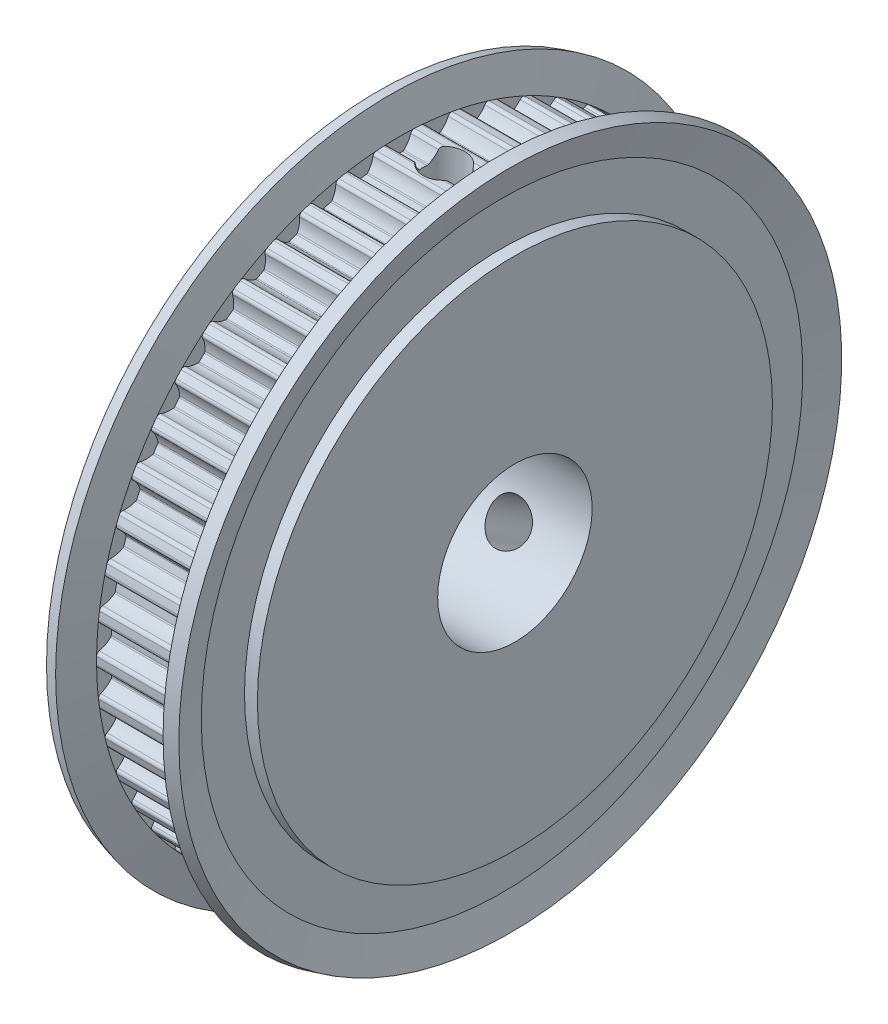
SolidWorks part; units mm, degrees
ref_plane "正面" through (0, 0, 0) normal (0, 0, 1) x (1, 0, 0)
ref_plane "平面" through (0, 0, 0) normal (0, 1, 0) x (1, 0, 0)
ref_plane "右側面" through (0, 0, 0) normal (1, 0, 0) x (0, 0, -1)
ref_plane "平面1" through (0, 0, 0) normal (0, 0, 1) x (1, 0, 0)
sketch "ｽｹｯﾁ1" plane through (0, 0, 0) normal (0, 0, 1) x (1, 0, 0)
  line L0 (0, 0) -> (0, 20)
  line L1 (0, 20) -> (1, 20)
  line L2 (1, 20) -> (1, 23.3583)
  line L3 (1, 23.3583) -> (0.3615, 25.7412)
  line L4 (0.3615, 25.7412) -> (1.3274, 26)
  line L5 (1.3274, 26) -> (2, 23.49)
  line L6 (2, 23.49) -> (9, 23.49)
  line L7 (9, 23.49) -> (9.6726, 26)
  line L8 (9.6726, 26) -> (10.6385, 25.7412)
  line L9 (10.6385, 25.7412) -> (10, 23.3583)
  line L10 (10, 23.3583) -> (10, 20)
  line L11 (10, 20) -> (11, 20)
  line L12 (11, 20) -> (11, 0)
  line L13 (11, 0) -> (0, 0)
  line L14 (11, 0) -> (0, 0) construction
revolve "回転1" add sketch "ｽｹｯﾁ1" angle 360 about L14
ref_plane "平面2" through (0, 0, 0) normal (0, 0, 1) x (1, 0, 0)
sketch "ｽｹｯﾁ2" plane through (0, 0, 0) normal (0, 0, 1) x (1, 0, 0)
  line L0 (0, 0) -> (0, 6)
  line L1 (0, 6) -> (11, 6)
  line L2 (11, 6) -> (11, 0)
  line L3 (11, 0) -> (0, 0)
  line L4 (11, 0) -> (0, 0) construction
revolve "ｶｯﾄ - 回転1" cut sketch "ｽｹｯﾁ2" angle 360 about L4
ref_plane "平面3" through (2, 0, 0) normal (1, 0, 0) x (0, 0, -1)
sketch "ｽｹｯﾁ3" plane through (2, 0, 0) normal (1, 0, 0) x (0, 0, -1)
  circle A0 centre (0, 0) radius 28.49
  arc A1 (-23.4883, 0.2846) -> (-23.4883, -0.2846) centre (0, 0) ccw
  arc A2 (-23.4883, -0.2846) -> (-23.2752, -0.5531) centre (-23.2083, -0.2812) ccw
  arc A3 (-23.2752, -0.5531) -> (-22.3989, -1.0274) centre (-23.7468, -2.4709) cw
  arc A4 (-22.3989, -1.0274) -> (-22.3515, -1.1295) centre (-22.5013, -1.137) cw
  arc A5 (-22.3515, -1.1295) -> (-22.3168, -1.6808) centre (0, 0) ccw
  arc A6 (-22.3168, -1.6808) -> (-22.3511, -1.788) centre (-22.4664, -1.6921) cw
  arc A7 (-22.3511, -1.788) -> (-23.1609, -2.3684) centre (-23.8692, -0.5248) cw
  arc A8 (-23.1609, -2.3684) -> (-23.3387, -2.6615) centre (-23.0605, -2.6298) ccw
  arc A9 (-23.3387, -2.6615) -> (-23.2674, -3.2262) centre (0, 0) ccw
  arc A10 (-23.2674, -3.2262) -> (-23.0223, -3.4659) centre (-22.99, -3.1877) ccw
  arc A11 (-23.0223, -3.4659) -> (-22.0935, -3.8266) centre (-23.2498, -5.4277) cw
  arc A12 (-22.0935, -3.8266) -> (-22.0337, -3.9219) centre (-22.1814, -3.9482) cw
  arc A13 (-22.0337, -3.9219) -> (-21.9302, -4.4646) centre (0, 0) ccw
  arc A14 (-21.9302, -4.4646) -> (-21.9507, -4.5753) centre (-22.0771, -4.4945) cw
  arc A15 (-21.9507, -4.5753) -> (-22.6815, -5.2526) centre (-23.6152, -3.5123) cw
  arc A16 (-22.6815, -5.2526) -> (-22.8211, -5.5657) centre (-22.5491, -5.4993) ccw
  arc A17 (-22.8211, -5.5657) -> (-22.6796, -6.1169) centre (0, 0) ccw
  arc A18 (-22.6796, -6.1169) -> (-22.4064, -6.324) centre (-22.4092, -6.044) ccw
  arc A19 (-22.4064, -6.324) -> (-21.4397, -6.5655) centre (-22.3862, -8.2989) cw
  arc A20 (-21.4397, -6.5655) -> (-21.3684, -6.6526) centre (-21.5116, -6.6971) cw
  arc A21 (-21.3684, -6.6526) -> (-21.1977, -7.178) centre (0, 0) ccw
  arc A22 (-21.1977, -7.178) -> (-21.2042, -7.2904) centre (-21.3397, -7.2261) cw
  arc A23 (-21.2042, -7.2904) -> (-21.8443, -8.0539) centre (-22.9888, -6.4443) cw
  arc A24 (-21.8443, -8.0539) -> (-21.9436, -8.382) centre (-21.682, -8.2821) ccw
  arc A25 (-21.9436, -8.382) -> (-21.7341, -8.9112) centre (0, 0) ccw
  arc A26 (-21.7341, -8.9112) -> (-21.4371, -9.0824) centre (-21.475, -8.805) ccw
  arc A27 (-21.4371, -9.0824) -> (-20.4478, -9.2008) centre (-21.1696, -11.0392) cw
  arc A28 (-20.4478, -9.2008) -> (-20.3661, -9.2783) centre (-20.5026, -9.3405) cw
  arc A29 (-20.3661, -9.2783) -> (-20.1309, -9.7782) centre (0, 0) ccw
  arc A30 (-20.1309, -9.7782) -> (-20.1233, -9.8905) centre (-20.2658, -9.8437) cw
  arc A31 (-20.1233, -9.8905) -> (-20.6626, -10.7282) centre (-21.9999, -9.2748) cw
  arc A32 (-20.6626, -10.7282) -> (-20.72, -11.0662) centre (-20.473, -10.9343) ccw
  arc A33 (-20.72, -11.0662) -> (-20.4458, -11.5649) centre (0, 0) ccw
  arc A34 (-20.4458, -11.5649) -> (-20.1297, -11.6976) centre (-20.2021, -11.4271) ccw
  arc A35 (-20.1297, -11.6976) -> (-19.1334, -11.6911) centre (-19.6191, -13.6054) cw
  arc A36 (-19.1334, -11.6911) -> (-19.0426, -11.7577) centre (-19.1703, -11.8365) cw
  arc A37 (-19.0426, -11.7577) -> (-18.7466, -12.2241) centre (0, 0) ccw
  arc A38 (-18.7466, -12.2241) -> (-18.725, -12.3346) centre (-18.8723, -12.3061) cw
  arc A39 (-18.725, -12.3346) -> (-19.1551, -13.2333) centre (-20.6639, -11.959) cw
  arc A40 (-19.1551, -13.2333) -> (-19.1697, -13.5758) centre (-18.9412, -13.414) ccw
  arc A41 (-19.1697, -13.5758) -> (-18.8351, -14.0363) centre (0, 0) ccw
  arc A42 (-18.8351, -14.0363) -> (-18.5049, -14.1283) centre (-18.6106, -13.869) ccw
  arc A43 (-18.5049, -14.1283) -> (-17.5172, -13.9969) centre (-17.7592, -15.9571) cw
  arc A44 (-17.5172, -13.9969) -> (-17.4189, -14.0516) centre (-17.5356, -14.1458) cw
  arc A45 (-17.4189, -14.0516) -> (-17.0667, -14.4773) centre (0, 0) ccw
  arc A46 (-17.0667, -14.4773) -> (-17.0314, -14.5842) centre (-17.1811, -14.5743) cw
  arc A47 (-17.0314, -14.5842) -> (-17.3455, -15.5298) centre (-19.0021, -14.4546) cw
  arc A48 (-17.3455, -15.5298) -> (-17.317, -15.8714) centre (-17.1106, -15.6822) ccw
  arc A49 (-17.317, -15.8714) -> (-16.9274, -16.2863) centre (0, 0) ccw
  arc A50 (-16.9274, -16.2863) -> (-16.5882, -16.3361) centre (-16.7256, -16.0922) ccw
  arc A51 (-16.5882, -16.3361) -> (-15.6248, -16.082) centre (-15.6192, -18.057) cw
  arc A52 (-15.6248, -16.082) -> (-15.5204, -16.124) centre (-15.6244, -16.232) cw
  arc A53 (-15.5204, -16.124) -> (-15.1176, -16.5022) centre (0, 0) ccw
  arc A54 (-15.1176, -16.5022) -> (-15.0692, -16.6038) centre (-15.219, -16.6128) cw
  arc A55 (-15.0692, -16.6038) -> (-15.2623, -17.5813) centre (-17.0407, -16.7222) cw
  arc A56 (-15.2623, -17.5813) -> (-15.1913, -17.9166) centre (-15.0102, -17.7031) ccw
  arc A57 (-15.1913, -17.9166) -> (-14.7527, -18.2794) centre (0, 0) ccw
  arc A58 (-14.7527, -18.2794) -> (-14.41, -18.2864) centre (-14.5769, -18.0615) ccw
  arc A59 (-14.41, -18.2864) -> (-13.486, -17.9135) centre (-13.2329, -19.8723) cw
  arc A60 (-13.486, -17.9135) -> (-13.3771, -17.9421) centre (-13.4668, -18.0623) cw
  arc A61 (-13.3771, -17.9421) -> (-12.9302, -18.2668) centre (0, 0) ccw
  arc A62 (-12.9302, -18.2668) -> (-12.8694, -18.3615) centre (-13.0168, -18.3892) cw
  arc A63 (-12.8694, -18.3615) -> (-12.9384, -19.3555) centre (-14.8105, -18.7261) cw
  arc A64 (-12.9384, -19.3555) -> (-12.8259, -19.6793) centre (-12.673, -19.4447) ccw
  arc A65 (-12.8259, -19.6793) -> (-12.3454, -19.9843) centre (0, 0) ccw
  arc A66 (-12.3454, -19.9843) -> (-12.0045, -19.9482) centre (-12.1982, -19.7461) ccw
  arc A67 (-12.0045, -19.9482) -> (-11.1345, -19.4625) centre (-10.6379, -21.3741) cw
  arc A68 (-11.1345, -19.4625) -> (-11.0229, -19.4772) centre (-11.0968, -19.6077) cw
  arc A69 (-11.0229, -19.4772) -> (-10.5388, -19.7433) centre (0, 0) ccw
  arc A70 (-10.5388, -19.7433) -> (-10.4666, -19.8297) centre (-10.6094, -19.8757) cw
  arc A71 (-10.4666, -19.8297) -> (-10.4105, -20.8245) centre (-12.3467, -20.4347) cw
  arc A72 (-10.4105, -20.8245) -> (-10.2583, -21.1317) centre (-10.136, -20.8798) ccw
  arc A73 (-10.2583, -21.1317) -> (-9.7433, -21.374) centre (0, 0) ccw
  arc A74 (-9.7433, -21.374) -> (-9.4096, -21.2955) centre (-9.6272, -21.1192) ccw
  arc A75 (-9.4096, -21.2955) -> (-8.6074, -20.7046) centre (-7.8751, -22.5388) cw
  arc A76 (-8.6074, -20.7046) -> (-8.4948, -20.7051) centre (-8.5518, -20.8439) cw
  arc A77 (-8.4948, -20.7051) -> (-7.9812, -20.9085) centre (0, 0) ccw
  arc A78 (-7.9812, -20.9085) -> (-7.8987, -20.9852) centre (-8.0347, -21.0486) cw
  arc A79 (-7.8987, -20.9852) -> (-7.7184, -21.9651) centre (-9.6882, -21.821) cw
  arc A80 (-7.7184, -21.9651) -> (-7.5289, -22.2507) centre (-7.4392, -21.9855) ccw
  arc A81 (-7.5289, -22.2507) -> (-6.9876, -22.4266) centre (0, 0) ccw
  arc A82 (-6.9876, -22.4266) -> (-6.6664, -22.3069) centre (-6.9043, -22.1593) ccw
  arc A83 (-6.6664, -22.3069) -> (-5.9445, -21.6201) centre (-4.9881, -23.3481) cw
  arc A84 (-5.9445, -21.6201) -> (-5.8328, -21.6065) centre (-5.8719, -21.7514) cw
  arc A85 (-5.8328, -21.6065) -> (-5.2977, -21.7439) centre (0, 0) ccw
  arc A86 (-5.2977, -21.7439) -> (-5.2063, -21.8097) centre (-5.3332, -21.8897) cw
  arc A87 (-5.2063, -21.8097) -> (-4.9046, -22.7593) centre (-6.8769, -22.8632) cw
  arc A88 (-4.9046, -22.7593) -> (-4.6808, -23.0189) centre (-4.625, -22.7445) ccw
  arc A89 (-4.6808, -23.0189) -> (-4.1217, -23.1256) centre (0, 0) ccw
  arc A90 (-4.1217, -23.1256) -> (-3.818, -22.9665) centre (-4.0726, -22.8499) ccw
  arc A91 (-3.818, -22.9665) -> (-3.188, -22.1947) centre (-2.0225, -23.7892) cw
  arc A92 (-3.188, -22.1947) -> (-3.0788, -22.1672) centre (-3.0994, -22.3158) cw
  arc A93 (-3.0788, -22.1672) -> (-2.5307, -22.2365) centre (0, 0) ccw
  arc A94 (-2.5307, -22.2365) -> (-2.4318, -22.2902) centre (-2.5476, -22.3855) cw
  arc A95 (-2.4318, -22.2902) -> (-2.0135, -23.1945) centre (-3.9571, -23.5448) cw
  arc A96 (-2.0135, -23.1945) -> (-1.7589, -23.4241) centre (-1.7379, -23.1448) ccw
  arc A97 (-1.7589, -23.4241) -> (-1.1908, -23.4598) centre (0, 0) ccw
  arc A98 (-1.1908, -23.4598) -> (-0.9095, -23.264) centre (-1.1766, -23.1802) ccw
  arc A99 (-0.9095, -23.264) -> (-0.3811, -22.4192) centre (0.975, -23.8551) cw
  arc A100 (-0.3811, -22.4192) -> (-0.2762, -22.3783) centre (-0.2781, -22.5283) cw
  arc A101 (-0.2762, -22.3783) -> (0.2762, -22.3783) centre (0, 0) ccw
  arc A102 (0.2762, -22.3783) -> (0.3811, -22.4192) centre (0.2781, -22.5283) cw
  arc A103 (0.3811, -22.4192) -> (0.9095, -23.264) centre (-0.975, -23.8551) cw
  arc A104 (0.9095, -23.264) -> (1.1908, -23.4598) centre (1.1766, -23.1802) ccw
  arc A105 (1.1908, -23.4598) -> (1.7589, -23.4241) centre (0, 0) ccw
  arc A106 (1.7589, -23.4241) -> (2.0135, -23.1945) centre (1.7379, -23.1448) ccw
  arc A107 (2.0135, -23.1945) -> (2.4318, -22.2902) centre (3.9571, -23.5448) cw
  arc A108 (2.4318, -22.2902) -> (2.5307, -22.2365) centre (2.5476, -22.3855) cw
  arc A109 (2.5307, -22.2365) -> (3.0788, -22.1672) centre (0, 0) ccw
  arc A110 (3.0788, -22.1672) -> (3.188, -22.1947) centre (3.0994, -22.3158) cw
  arc A111 (3.188, -22.1947) -> (3.818, -22.9665) centre (2.0225, -23.7892) cw
  arc A112 (3.818, -22.9665) -> (4.1217, -23.1256) centre (4.0726, -22.8499) ccw
  arc A113 (4.1217, -23.1256) -> (4.6808, -23.0189) centre (0, 0) ccw
  arc A114 (4.6808, -23.0189) -> (4.9046, -22.7593) centre (4.625, -22.7445) ccw
  arc A115 (4.9046, -22.7593) -> (5.2063, -21.8097) centre (6.8769, -22.8632) cw
  arc A116 (5.2063, -21.8097) -> (5.2977, -21.7439) centre (5.3332, -21.8897) cw
  arc A117 (5.2977, -21.7439) -> (5.8328, -21.6065) centre (0, 0) ccw
  arc A118 (5.8328, -21.6065) -> (5.9445, -21.6201) centre (5.8719, -21.7514) cw
  arc A119 (5.9445, -21.6201) -> (6.6664, -22.3069) centre (4.9881, -23.3481) cw
  arc A120 (6.6664, -22.3069) -> (6.9876, -22.4266) centre (6.9043, -22.1593) ccw
  arc A121 (6.9876, -22.4266) -> (7.5289, -22.2507) centre (0, 0) ccw
  arc A122 (7.5289, -22.2507) -> (7.7184, -21.9651) centre (7.4392, -21.9855) ccw
  arc A123 (7.7184, -21.9651) -> (7.8987, -20.9852) centre (9.6882, -21.821) cw
  arc A124 (7.8987, -20.9852) -> (7.9812, -20.9085) centre (8.0347, -21.0486) cw
  arc A125 (7.9812, -20.9085) -> (8.4948, -20.7051) centre (0, 0) ccw
  arc A126 (8.4948, -20.7051) -> (8.6074, -20.7046) centre (8.5518, -20.8439) cw
  arc A127 (8.6074, -20.7046) -> (9.4096, -21.2955) centre (7.8751, -22.5388) cw
  arc A128 (9.4096, -21.2955) -> (9.7433, -21.374) centre (9.6272, -21.1192) ccw
  arc A129 (9.7433, -21.374) -> (10.2583, -21.1317) centre (0, 0) ccw
  arc A130 (10.2583, -21.1317) -> (10.4105, -20.8245) centre (10.136, -20.8798) ccw
  arc A131 (10.4105, -20.8245) -> (10.4666, -19.8297) centre (12.3467, -20.4347) cw
  arc A132 (10.4666, -19.8297) -> (10.5388, -19.7433) centre (10.6094, -19.8757) cw
  arc A133 (10.5388, -19.7433) -> (11.0229, -19.4772) centre (0, 0) ccw
  arc A134 (11.0229, -19.4772) -> (11.1345, -19.4625) centre (11.0968, -19.6077) cw
  arc A135 (11.1345, -19.4625) -> (12.0045, -19.9482) centre (10.6379, -21.3741) cw
  arc A136 (12.0045, -19.9482) -> (12.3454, -19.9843) centre (12.1982, -19.7461) ccw
  arc A137 (12.3454, -19.9843) -> (12.8259, -19.6793) centre (0, 0) ccw
  arc A138 (12.8259, -19.6793) -> (12.9384, -19.3555) centre (12.673, -19.4447) ccw
  arc A139 (12.9384, -19.3555) -> (12.8694, -18.3615) centre (14.8105, -18.7261) cw
  arc A140 (12.8694, -18.3615) -> (12.9302, -18.2668) centre (13.0168, -18.3892) cw
  arc A141 (12.9302, -18.2668) -> (13.3771, -17.9421) centre (0, 0) ccw
  arc A142 (13.3771, -17.9421) -> (13.486, -17.9135) centre (13.4668, -18.0623) cw
  arc A143 (13.486, -17.9135) -> (14.41, -18.2864) centre (13.2329, -19.8723) cw
  arc A144 (14.41, -18.2864) -> (14.7527, -18.2794) centre (14.5769, -18.0615) ccw
  arc A145 (14.7527, -18.2794) -> (15.1913, -17.9166) centre (0, 0) ccw
  arc A146 (15.1913, -17.9166) -> (15.2623, -17.5813) centre (15.0102, -17.7031) ccw
  arc A147 (15.2623, -17.5813) -> (15.0692, -16.6038) centre (17.0407, -16.7222) cw
  arc A148 (15.0692, -16.6038) -> (15.1176, -16.5022) centre (15.219, -16.6128) cw
  arc A149 (15.1176, -16.5022) -> (15.5204, -16.124) centre (0, 0) ccw
  arc A150 (15.5204, -16.124) -> (15.6248, -16.082) centre (15.6244, -16.232) cw
  arc A151 (15.6248, -16.082) -> (16.5882, -16.3361) centre (15.6192, -18.057) cw
  arc A152 (16.5882, -16.3361) -> (16.9274, -16.2863) centre (16.7256, -16.0922) ccw
  arc A153 (16.9274, -16.2863) -> (17.317, -15.8714) centre (0, 0) ccw
  arc A154 (17.317, -15.8714) -> (17.3455, -15.5298) centre (17.1106, -15.6822) ccw
  arc A155 (17.3455, -15.5298) -> (17.0314, -14.5842) centre (19.0021, -14.4546) cw
  arc A156 (17.0314, -14.5842) -> (17.0667, -14.4773) centre (17.1811, -14.5743) cw
  arc A157 (17.0667, -14.4773) -> (17.4189, -14.0516) centre (0, 0) ccw
  arc A158 (17.4189, -14.0516) -> (17.5172, -13.9969) centre (17.5356, -14.1458) cw
  arc A159 (17.5172, -13.9969) -> (18.5049, -14.1283) centre (17.7592, -15.9571) cw
  arc A160 (18.5049, -14.1283) -> (18.8351, -14.0363) centre (18.6106, -13.869) ccw
  arc A161 (18.8351, -14.0363) -> (19.1697, -13.5758) centre (0, 0) ccw
  arc A162 (19.1697, -13.5758) -> (19.1551, -13.2333) centre (18.9412, -13.414) ccw
  arc A163 (19.1551, -13.2333) -> (18.725, -12.3346) centre (20.6639, -11.959) cw
  arc A164 (18.725, -12.3346) -> (18.7466, -12.2241) centre (18.8723, -12.3061) cw
  arc A165 (18.7466, -12.2241) -> (19.0426, -11.7577) centre (0, 0) ccw
  arc A166 (19.0426, -11.7577) -> (19.1334, -11.6911) centre (19.1703, -11.8365) cw
  arc A167 (19.1334, -11.6911) -> (20.1297, -11.6976) centre (19.6191, -13.6054) cw
  arc A168 (20.1297, -11.6976) -> (20.4458, -11.5649) centre (20.2021, -11.4271) ccw
  arc A169 (20.4458, -11.5649) -> (20.72, -11.0662) centre (0, 0) ccw
  arc A170 (20.72, -11.0662) -> (20.6626, -10.7282) centre (20.473, -10.9343) ccw
  arc A171 (20.6626, -10.7282) -> (20.1233, -9.8905) centre (21.9999, -9.2748) cw
  arc A172 (20.1233, -9.8905) -> (20.1309, -9.7782) centre (20.2658, -9.8437) cw
  arc A173 (20.1309, -9.7782) -> (20.3661, -9.2783) centre (0, 0) ccw
  arc A174 (20.3661, -9.2783) -> (20.4478, -9.2008) centre (20.5026, -9.3405) cw
  arc A175 (20.4478, -9.2008) -> (21.4371, -9.0824) centre (21.1696, -11.0392) cw
  arc A176 (21.4371, -9.0824) -> (21.7341, -8.9112) centre (21.475, -8.805) ccw
  arc A177 (21.7341, -8.9112) -> (21.9436, -8.382) centre (0, 0) ccw
  arc A178 (21.9436, -8.382) -> (21.8443, -8.0539) centre (21.682, -8.2821) ccw
  arc A179 (21.8443, -8.0539) -> (21.2042, -7.2904) centre (22.9888, -6.4443) cw
  arc A180 (21.2042, -7.2904) -> (21.1977, -7.178) centre (21.3397, -7.2261) cw
  arc A181 (21.1977, -7.178) -> (21.3684, -6.6526) centre (0, 0) ccw
  arc A182 (21.3684, -6.6526) -> (21.4397, -6.5655) centre (21.5116, -6.6971) cw
  arc A183 (21.4397, -6.5655) -> (22.4064, -6.324) centre (22.3862, -8.2989) cw
  arc A184 (22.4064, -6.324) -> (22.6796, -6.1169) centre (22.4092, -6.044) ccw
  arc A185 (22.6796, -6.1169) -> (22.8211, -5.5657) centre (0, 0) ccw
  arc A186 (22.8211, -5.5657) -> (22.6815, -5.2526) centre (22.5491, -5.4993) ccw
  arc A187 (22.6815, -5.2526) -> (21.9507, -4.5753) centre (23.6152, -3.5123) cw
  arc A188 (21.9507, -4.5753) -> (21.9302, -4.4646) centre (22.0771, -4.4945) cw
  arc A189 (21.9302, -4.4646) -> (22.0337, -3.9219) centre (0, 0) ccw
  arc A190 (22.0337, -3.9219) -> (22.0935, -3.8266) centre (22.1814, -3.9482) cw
  arc A191 (22.0935, -3.8266) -> (23.0223, -3.4659) centre (23.2498, -5.4277) cw
  arc A192 (23.0223, -3.4659) -> (23.2674, -3.2262) centre (22.99, -3.1877) ccw
  arc A193 (23.2674, -3.2262) -> (23.3387, -2.6615) centre (0, 0) ccw
  arc A194 (23.3387, -2.6615) -> (23.1609, -2.3684) centre (23.0605, -2.6298) ccw
  arc A195 (23.1609, -2.3684) -> (22.3511, -1.788) centre (23.8692, -0.5248) cw
  arc A196 (22.3511, -1.788) -> (22.3168, -1.6808) centre (22.4664, -1.6921) cw
  arc A197 (22.3168, -1.6808) -> (22.3515, -1.1295) centre (0, 0) ccw
  arc A198 (22.3515, -1.1295) -> (22.3989, -1.0274) centre (22.5013, -1.137) cw
  arc A199 (22.3989, -1.0274) -> (23.2752, -0.5531) centre (23.7468, -2.4709) cw
  arc A200 (23.2752, -0.5531) -> (23.4883, -0.2846) centre (23.2083, -0.2812) ccw
  arc A201 (23.4883, -0.2846) -> (23.4883, 0.2846) centre (0, 0) ccw
  arc A202 (23.4883, 0.2846) -> (23.2752, 0.5531) centre (23.2083, 0.2812) ccw
  arc A203 (23.2752, 0.5531) -> (22.3989, 1.0274) centre (23.7468, 2.4709) cw
  arc A204 (22.3989, 1.0274) -> (22.3515, 1.1295) centre (22.5013, 1.137) cw
  arc A205 (22.3515, 1.1295) -> (22.3168, 1.6808) centre (0, 0) ccw
  arc A206 (22.3168, 1.6808) -> (22.3511, 1.788) centre (22.4664, 1.6921) cw
  arc A207 (22.3511, 1.788) -> (23.1609, 2.3684) centre (23.8692, 0.5248) cw
  arc A208 (23.1609, 2.3684) -> (23.3387, 2.6615) centre (23.0605, 2.6298) ccw
  arc A209 (23.3387, 2.6615) -> (23.2674, 3.2262) centre (0, 0) ccw
  arc A210 (23.2674, 3.2262) -> (23.0223, 3.4659) centre (22.99, 3.1877) ccw
  arc A211 (23.0223, 3.4659) -> (22.0935, 3.8266) centre (23.2498, 5.4277) cw
  arc A212 (22.0935, 3.8266) -> (22.0337, 3.9219) centre (22.1814, 3.9482) cw
  arc A213 (22.0337, 3.9219) -> (21.9302, 4.4646) centre (0, 0) ccw
  arc A214 (21.9302, 4.4646) -> (21.9507, 4.5753) centre (22.0771, 4.4945) cw
  arc A215 (21.9507, 4.5753) -> (22.6815, 5.2526) centre (23.6152, 3.5123) cw
  arc A216 (22.6815, 5.2526) -> (22.8211, 5.5657) centre (22.5491, 5.4993) ccw
  arc A217 (22.8211, 5.5657) -> (22.6796, 6.1169) centre (0, 0) ccw
  arc A218 (22.6796, 6.1169) -> (22.4064, 6.324) centre (22.4092, 6.044) ccw
  arc A219 (22.4064, 6.324) -> (21.4397, 6.5655) centre (22.3862, 8.2989) cw
  arc A220 (21.4397, 6.5655) -> (21.3684, 6.6526) centre (21.5116, 6.6971) cw
  arc A221 (21.3684, 6.6526) -> (21.1977, 7.178) centre (0, 0) ccw
  arc A222 (21.1977, 7.178) -> (21.2042, 7.2904) centre (21.3397, 7.2261) cw
  arc A223 (21.2042, 7.2904) -> (21.8443, 8.0539) centre (22.9888, 6.4443) cw
  arc A224 (21.8443, 8.0539) -> (21.9436, 8.382) centre (21.682, 8.2821) ccw
  arc A225 (21.9436, 8.382) -> (21.7341, 8.9112) centre (0, 0) ccw
  arc A226 (21.7341, 8.9112) -> (21.4371, 9.0824) centre (21.475, 8.805) ccw
  arc A227 (21.4371, 9.0824) -> (20.4478, 9.2008) centre (21.1696, 11.0392) cw
  arc A228 (20.4478, 9.2008) -> (20.3661, 9.2783) centre (20.5026, 9.3405) cw
  arc A229 (20.3661, 9.2783) -> (20.1309, 9.7782) centre (0, 0) ccw
  arc A230 (20.1309, 9.7782) -> (20.1233, 9.8905) centre (20.2658, 9.8437) cw
  arc A231 (20.1233, 9.8905) -> (20.6626, 10.7282) centre (21.9999, 9.2748) cw
  arc A232 (20.6626, 10.7282) -> (20.72, 11.0662) centre (20.473, 10.9343) ccw
  arc A233 (20.72, 11.0662) -> (20.4458, 11.5649) centre (0, 0) ccw
  arc A234 (20.4458, 11.5649) -> (20.1297, 11.6976) centre (20.2021, 11.4271) ccw
  arc A235 (20.1297, 11.6976) -> (19.1334, 11.6911) centre (19.6191, 13.6054) cw
  arc A236 (19.1334, 11.6911) -> (19.0426, 11.7577) centre (19.1703, 11.8365) cw
  arc A237 (19.0426, 11.7577) -> (18.7466, 12.2241) centre (0, 0) ccw
  arc A238 (18.7466, 12.2241) -> (18.725, 12.3346) centre (18.8723, 12.3061) cw
  arc A239 (18.725, 12.3346) -> (19.1551, 13.2333) centre (20.6639, 11.959) cw
  arc A240 (19.1551, 13.2333) -> (19.1697, 13.5758) centre (18.9412, 13.414) ccw
  arc A241 (19.1697, 13.5758) -> (18.8351, 14.0363) centre (0, 0) ccw
  arc A242 (18.8351, 14.0363) -> (18.5049, 14.1283) centre (18.6106, 13.869) ccw
  arc A243 (18.5049, 14.1283) -> (17.5172, 13.9969) centre (17.7592, 15.9571) cw
  arc A244 (17.5172, 13.9969) -> (17.4189, 14.0516) centre (17.5356, 14.1458) cw
  arc A245 (17.4189, 14.0516) -> (17.0667, 14.4773) centre (0, 0) ccw
  arc A246 (17.0667, 14.4773) -> (17.0314, 14.5842) centre (17.1811, 14.5743) cw
  arc A247 (17.0314, 14.5842) -> (17.3455, 15.5298) centre (19.0021, 14.4546) cw
  arc A248 (17.3455, 15.5298) -> (17.317, 15.8714) centre (17.1106, 15.6822) ccw
  arc A249 (17.317, 15.8714) -> (16.9274, 16.2863) centre (0, 0) ccw
  arc A250 (16.9274, 16.2863) -> (16.5882, 16.3361) centre (16.7256, 16.0922) ccw
  arc A251 (16.5882, 16.3361) -> (15.6248, 16.082) centre (15.6192, 18.057) cw
  arc A252 (15.6248, 16.082) -> (15.5204, 16.124) centre (15.6244, 16.232) cw
  arc A253 (15.5204, 16.124) -> (15.1176, 16.5022) centre (0, 0) ccw
  arc A254 (15.1176, 16.5022) -> (15.0692, 16.6038) centre (15.219, 16.6128) cw
  arc A255 (15.0692, 16.6038) -> (15.2623, 17.5813) centre (17.0407, 16.7222) cw
  arc A256 (15.2623, 17.5813) -> (15.1913, 17.9166) centre (15.0102, 17.7031) ccw
  arc A257 (15.1913, 17.9166) -> (14.7527, 18.2794) centre (0, 0) ccw
  arc A258 (14.7527, 18.2794) -> (14.41, 18.2864) centre (14.5769, 18.0615) ccw
  arc A259 (14.41, 18.2864) -> (13.486, 17.9135) centre (13.2329, 19.8723) cw
  arc A260 (13.486, 17.9135) -> (13.3771, 17.9421) centre (13.4668, 18.0623) cw
  arc A261 (13.3771, 17.9421) -> (12.9302, 18.2668) centre (0, 0) ccw
  arc A262 (12.9302, 18.2668) -> (12.8694, 18.3615) centre (13.0168, 18.3892) cw
  arc A263 (12.8694, 18.3615) -> (12.9384, 19.3555) centre (14.8105, 18.7261) cw
  arc A264 (12.9384, 19.3555) -> (12.8259, 19.6793) centre (12.673, 19.4447) ccw
  arc A265 (12.8259, 19.6793) -> (12.3454, 19.9843) centre (0, 0) ccw
  arc A266 (12.3454, 19.9843) -> (12.0045, 19.9482) centre (12.1982, 19.7461) ccw
  arc A267 (12.0045, 19.9482) -> (11.1345, 19.4625) centre (10.6379, 21.3741) cw
  arc A268 (11.1345, 19.4625) -> (11.0229, 19.4772) centre (11.0968, 19.6077) cw
  arc A269 (11.0229, 19.4772) -> (10.5388, 19.7433) centre (0, 0) ccw
  arc A270 (10.5388, 19.7433) -> (10.4666, 19.8297) centre (10.6094, 19.8757) cw
  arc A271 (10.4666, 19.8297) -> (10.4105, 20.8245) centre (12.3467, 20.4347) cw
  arc A272 (10.4105, 20.8245) -> (10.2583, 21.1317) centre (10.136, 20.8798) ccw
  arc A273 (10.2583, 21.1317) -> (9.7433, 21.374) centre (0, 0) ccw
  arc A274 (9.7433, 21.374) -> (9.4096, 21.2955) centre (9.6272, 21.1192) ccw
  arc A275 (9.4096, 21.2955) -> (8.6074, 20.7046) centre (7.8751, 22.5388) cw
  arc A276 (8.6074, 20.7046) -> (8.4948, 20.7051) centre (8.5518, 20.8439) cw
  arc A277 (8.4948, 20.7051) -> (7.9812, 20.9085) centre (0, 0) ccw
  arc A278 (7.9812, 20.9085) -> (7.8987, 20.9852) centre (8.0347, 21.0486) cw
  arc A279 (7.8987, 20.9852) -> (7.7184, 21.9651) centre (9.6882, 21.821) cw
  arc A280 (7.7184, 21.9651) -> (7.5289, 22.2507) centre (7.4392, 21.9855) ccw
  arc A281 (7.5289, 22.2507) -> (6.9876, 22.4266) centre (0, 0) ccw
  arc A282 (6.9876, 22.4266) -> (6.6664, 22.3069) centre (6.9043, 22.1593) ccw
  arc A283 (6.6664, 22.3069) -> (5.9445, 21.6201) centre (4.9881, 23.3481) cw
  arc A284 (5.9445, 21.6201) -> (5.8328, 21.6065) centre (5.8719, 21.7514) cw
  arc A285 (5.8328, 21.6065) -> (5.2977, 21.7439) centre (0, 0) ccw
  arc A286 (5.2977, 21.7439) -> (5.2063, 21.8097) centre (5.3332, 21.8897) cw
  arc A287 (5.2063, 21.8097) -> (4.9046, 22.7593) centre (6.8769, 22.8632) cw
  arc A288 (4.9046, 22.7593) -> (4.6808, 23.0189) centre (4.625, 22.7445) ccw
  arc A289 (4.6808, 23.0189) -> (4.1217, 23.1256) centre (0, 0) ccw
  arc A290 (4.1217, 23.1256) -> (3.818, 22.9665) centre (4.0726, 22.8499) ccw
  arc A291 (3.818, 22.9665) -> (3.188, 22.1947) centre (2.0225, 23.7892) cw
  arc A292 (3.188, 22.1947) -> (3.0788, 22.1672) centre (3.0994, 22.3158) cw
  arc A293 (3.0788, 22.1672) -> (2.5307, 22.2365) centre (0, 0) ccw
  arc A294 (2.5307, 22.2365) -> (2.4318, 22.2902) centre (2.5476, 22.3855) cw
  arc A295 (2.4318, 22.2902) -> (2.0135, 23.1945) centre (3.9571, 23.5448) cw
  arc A296 (2.0135, 23.1945) -> (1.7589, 23.4241) centre (1.7379, 23.1448) ccw
  arc A297 (1.7589, 23.4241) -> (1.1908, 23.4598) centre (0, 0) ccw
  arc A298 (1.1908, 23.4598) -> (0.9095, 23.264) centre (1.1766, 23.1802) ccw
  arc A299 (0.9095, 23.264) -> (0.3811, 22.4192) centre (-0.975, 23.8551) cw
  arc A300 (0.3811, 22.4192) -> (0.2762, 22.3783) centre (0.2781, 22.5283) cw
  arc A301 (0.2762, 22.3783) -> (-0.2762, 22.3783) centre (0, 0) ccw
  arc A302 (-0.2762, 22.3783) -> (-0.3811, 22.4192) centre (-0.2781, 22.5283) cw
  arc A303 (-0.3811, 22.4192) -> (-0.9095, 23.264) centre (0.975, 23.8551) cw
  arc A304 (-0.9095, 23.264) -> (-1.1908, 23.4598) centre (-1.1766, 23.1802) ccw
  arc A305 (-1.1908, 23.4598) -> (-1.7589, 23.4241) centre (0, 0) ccw
  arc A306 (-1.7589, 23.4241) -> (-2.0135, 23.1945) centre (-1.7379, 23.1448) ccw
  arc A307 (-2.0135, 23.1945) -> (-2.4318, 22.2902) centre (-3.9571, 23.5448) cw
  arc A308 (-2.4318, 22.2902) -> (-2.5307, 22.2365) centre (-2.5476, 22.3855) cw
  arc A309 (-2.5307, 22.2365) -> (-3.0788, 22.1672) centre (0, 0) ccw
  arc A310 (-3.0788, 22.1672) -> (-3.188, 22.1947) centre (-3.0994, 22.3158) cw
  arc A311 (-3.188, 22.1947) -> (-3.818, 22.9665) centre (-2.0225, 23.7892) cw
  arc A312 (-3.818, 22.9665) -> (-4.1217, 23.1256) centre (-4.0726, 22.8499) ccw
  arc A313 (-4.1217, 23.1256) -> (-4.6808, 23.0189) centre (0, 0) ccw
  arc A314 (-4.6808, 23.0189) -> (-4.9046, 22.7593) centre (-4.625, 22.7445) ccw
  arc A315 (-4.9046, 22.7593) -> (-5.2063, 21.8097) centre (-6.8769, 22.8632) cw
  arc A316 (-5.2063, 21.8097) -> (-5.2977, 21.7439) centre (-5.3332, 21.8897) cw
  arc A317 (-5.2977, 21.7439) -> (-5.8328, 21.6065) centre (0, 0) ccw
  arc A318 (-5.8328, 21.6065) -> (-5.9445, 21.6201) centre (-5.8719, 21.7514) cw
  arc A319 (-5.9445, 21.6201) -> (-6.6664, 22.3069) centre (-4.9881, 23.3481) cw
  arc A320 (-6.6664, 22.3069) -> (-6.9876, 22.4266) centre (-6.9043, 22.1593) ccw
  arc A321 (-6.9876, 22.4266) -> (-7.5289, 22.2507) centre (0, 0) ccw
  arc A322 (-7.5289, 22.2507) -> (-7.7184, 21.9651) centre (-7.4392, 21.9855) ccw
  arc A323 (-7.7184, 21.9651) -> (-7.8987, 20.9852) centre (-9.6882, 21.821) cw
  arc A324 (-7.8987, 20.9852) -> (-7.9812, 20.9085) centre (-8.0347, 21.0486) cw
  arc A325 (-7.9812, 20.9085) -> (-8.4948, 20.7051) centre (0, 0) ccw
  arc A326 (-8.4948, 20.7051) -> (-8.6074, 20.7046) centre (-8.5518, 20.8439) cw
  arc A327 (-8.6074, 20.7046) -> (-9.4096, 21.2955) centre (-7.8751, 22.5388) cw
  arc A328 (-9.4096, 21.2955) -> (-9.7433, 21.374) centre (-9.6272, 21.1192) ccw
  arc A329 (-9.7433, 21.374) -> (-10.2583, 21.1317) centre (0, 0) ccw
  arc A330 (-10.2583, 21.1317) -> (-10.4105, 20.8245) centre (-10.136, 20.8798) ccw
  arc A331 (-10.4105, 20.8245) -> (-10.4666, 19.8297) centre (-12.3467, 20.4347) cw
  arc A332 (-10.4666, 19.8297) -> (-10.5388, 19.7433) centre (-10.6094, 19.8757) cw
  arc A333 (-10.5388, 19.7433) -> (-11.0229, 19.4772) centre (0, 0) ccw
  arc A334 (-11.0229, 19.4772) -> (-11.1345, 19.4625) centre (-11.0968, 19.6077) cw
  arc A335 (-11.1345, 19.4625) -> (-12.0045, 19.9482) centre (-10.6379, 21.3741) cw
  arc A336 (-12.0045, 19.9482) -> (-12.3454, 19.9843) centre (-12.1982, 19.7461) ccw
  arc A337 (-12.3454, 19.9843) -> (-12.8259, 19.6793) centre (0, 0) ccw
  arc A338 (-12.8259, 19.6793) -> (-12.9384, 19.3555) centre (-12.673, 19.4447) ccw
  arc A339 (-12.9384, 19.3555) -> (-12.8694, 18.3615) centre (-14.8105, 18.7261) cw
  arc A340 (-12.8694, 18.3615) -> (-12.9302, 18.2668) centre (-13.0168, 18.3892) cw
  arc A341 (-12.9302, 18.2668) -> (-13.3771, 17.9421) centre (0, 0) ccw
  arc A342 (-13.3771, 17.9421) -> (-13.486, 17.9135) centre (-13.4668, 18.0623) cw
  arc A343 (-13.486, 17.9135) -> (-14.41, 18.2864) centre (-13.2329, 19.8723) cw
  arc A344 (-14.41, 18.2864) -> (-14.7527, 18.2794) centre (-14.5769, 18.0615) ccw
  arc A345 (-14.7527, 18.2794) -> (-15.1913, 17.9166) centre (0, 0) ccw
  arc A346 (-15.1913, 17.9166) -> (-15.2623, 17.5813) centre (-15.0102, 17.7031) ccw
  arc A347 (-15.2623, 17.5813) -> (-15.0692, 16.6038) centre (-17.0407, 16.7222) cw
  arc A348 (-15.0692, 16.6038) -> (-15.1176, 16.5022) centre (-15.219, 16.6128) cw
  arc A349 (-15.1176, 16.5022) -> (-15.5204, 16.124) centre (0, 0) ccw
  arc A350 (-15.5204, 16.124) -> (-15.6248, 16.082) centre (-15.6244, 16.232) cw
  arc A351 (-15.6248, 16.082) -> (-16.5882, 16.3361) centre (-15.6192, 18.057) cw
  arc A352 (-16.5882, 16.3361) -> (-16.9274, 16.2863) centre (-16.7256, 16.0922) ccw
  arc A353 (-16.9274, 16.2863) -> (-17.317, 15.8714) centre (0, 0) ccw
  arc A354 (-17.317, 15.8714) -> (-17.3455, 15.5298) centre (-17.1106, 15.6822) ccw
  arc A355 (-17.3455, 15.5298) -> (-17.0314, 14.5842) centre (-19.0021, 14.4546) cw
  arc A356 (-17.0314, 14.5842) -> (-17.0667, 14.4773) centre (-17.1811, 14.5743) cw
  arc A357 (-17.0667, 14.4773) -> (-17.4189, 14.0516) centre (0, 0) ccw
  arc A358 (-17.4189, 14.0516) -> (-17.5172, 13.9969) centre (-17.5356, 14.1458) cw
  arc A359 (-17.5172, 13.9969) -> (-18.5049, 14.1283) centre (-17.7592, 15.9571) cw
  arc A360 (-18.5049, 14.1283) -> (-18.8351, 14.0363) centre (-18.6106, 13.869) ccw
  arc A361 (-18.8351, 14.0363) -> (-19.1697, 13.5758) centre (0, 0) ccw
  arc A362 (-19.1697, 13.5758) -> (-19.1551, 13.2333) centre (-18.9412, 13.414) ccw
  arc A363 (-19.1551, 13.2333) -> (-18.725, 12.3346) centre (-20.6639, 11.959) cw
  arc A364 (-18.725, 12.3346) -> (-18.7466, 12.2241) centre (-18.8723, 12.3061) cw
  arc A365 (-18.7466, 12.2241) -> (-19.0426, 11.7577) centre (0, 0) ccw
  arc A366 (-19.0426, 11.7577) -> (-19.1334, 11.6911) centre (-19.1703, 11.8365) cw
  arc A367 (-19.1334, 11.6911) -> (-20.1297, 11.6976) centre (-19.6191, 13.6054) cw
  arc A368 (-20.1297, 11.6976) -> (-20.4458, 11.5649) centre (-20.2021, 11.4271) ccw
  arc A369 (-20.4458, 11.5649) -> (-20.72, 11.0662) centre (0, 0) ccw
  arc A370 (-20.72, 11.0662) -> (-20.6626, 10.7282) centre (-20.473, 10.9343) ccw
  arc A371 (-20.6626, 10.7282) -> (-20.1233, 9.8905) centre (-21.9999, 9.2748) cw
  arc A372 (-20.1233, 9.8905) -> (-20.1309, 9.7782) centre (-20.2658, 9.8437) cw
  arc A373 (-20.1309, 9.7782) -> (-20.3661, 9.2783) centre (0, 0) ccw
  arc A374 (-20.3661, 9.2783) -> (-20.4478, 9.2008) centre (-20.5026, 9.3405) cw
  arc A375 (-20.4478, 9.2008) -> (-21.4371, 9.0824) centre (-21.1696, 11.0392) cw
  arc A376 (-21.4371, 9.0824) -> (-21.7341, 8.9112) centre (-21.475, 8.805) ccw
  arc A377 (-21.7341, 8.9112) -> (-21.9436, 8.382) centre (0, 0) ccw
  arc A378 (-21.9436, 8.382) -> (-21.8443, 8.0539) centre (-21.682, 8.2821) ccw
  arc A379 (-21.8443, 8.0539) -> (-21.2042, 7.2904) centre (-22.9888, 6.4443) cw
  arc A380 (-21.2042, 7.2904) -> (-21.1977, 7.178) centre (-21.3397, 7.2261) cw
  arc A381 (-21.1977, 7.178) -> (-21.3684, 6.6526) centre (0, 0) ccw
  arc A382 (-21.3684, 6.6526) -> (-21.4397, 6.5655) centre (-21.5116, 6.6971) cw
  arc A383 (-21.4397, 6.5655) -> (-22.4064, 6.324) centre (-22.3862, 8.2989) cw
  arc A384 (-22.4064, 6.324) -> (-22.6796, 6.1169) centre (-22.4092, 6.044) ccw
  arc A385 (-22.6796, 6.1169) -> (-22.8211, 5.5657) centre (0, 0) ccw
  arc A386 (-22.8211, 5.5657) -> (-22.6815, 5.2526) centre (-22.5491, 5.4993) ccw
  arc A387 (-22.6815, 5.2526) -> (-21.9507, 4.5753) centre (-23.6152, 3.5123) cw
  arc A388 (-21.9507, 4.5753) -> (-21.9302, 4.4646) centre (-22.0771, 4.4945) cw
  arc A389 (-21.9302, 4.4646) -> (-22.0337, 3.9219) centre (0, 0) ccw
  arc A390 (-22.0337, 3.9219) -> (-22.0935, 3.8266) centre (-22.1814, 3.9482) cw
  arc A391 (-22.0935, 3.8266) -> (-23.0223, 3.4659) centre (-23.2498, 5.4277) cw
  arc A392 (-23.0223, 3.4659) -> (-23.2674, 3.2262) centre (-22.99, 3.1877) ccw
  arc A393 (-23.2674, 3.2262) -> (-23.3387, 2.6615) centre (0, 0) ccw
  arc A394 (-23.3387, 2.6615) -> (-23.1609, 2.3684) centre (-23.0605, 2.6298) ccw
  arc A395 (-23.1609, 2.3684) -> (-22.3511, 1.788) centre (-23.8692, 0.5248) cw
  arc A396 (-22.3511, 1.788) -> (-22.3168, 1.6808) centre (-22.4664, 1.6921) cw
  arc A397 (-22.3168, 1.6808) -> (-22.3515, 1.1295) centre (0, 0) ccw
  arc A398 (-22.3515, 1.1295) -> (-22.3989, 1.0274) centre (-22.5013, 1.137) cw
  arc A399 (-22.3989, 1.0274) -> (-23.2752, 0.5531) centre (-23.7468, 2.4709) cw
  arc A400 (-23.2752, 0.5531) -> (-23.4883, 0.2846) centre (-23.2083, 0.2812) ccw
extrude "ｶｯﾄ - 押し出し1" cut sketch "ｽｹｯﾁ3" along normal blind 7
ref_plane "平面4" through (5.5, 0, 0) normal (1, 0, 0) x (0, 0, -1)
sketch "ｽｹｯﾁ4" plane through (5.5, 0, 0) normal (1, 0, 0) x (0, 0, -1)
  line L0 (0, 23.49) -> (1.621, 23.49)
  line L1 (1.621, 23.49) -> (1.621, 0)
  line L2 (1.621, 0) -> (0, 0)
  line L3 (0, 0) -> (0, 23.49)
  line L4 (0, 0) -> (0, 23.49) construction
revolve "ｶｯﾄ - 回転2" cut sketch "ｽｹｯﾁ4" angle 360 about L4
ref_plane "平面5" through (5.5, 0, 0) normal (1, 0, 0) x (0, 0, -1)
sketch "ｽｹｯﾁ5" plane through (5.5, 0, 0) normal (1, 0, 0) x (0, 0, -1)
  line L0 (19.8333, -12.5866) -> (18.9647, -13.9552)
  line L1 (18.9647, -13.9552) -> (-0.8686, -1.3687)
  line L2 (-0.8686, -1.3687) -> (0, 0)
  line L3 (0, 0) -> (19.8333, -12.5866)
  line L4 (0, 0) -> (19.8333, -12.5866) construction
revolve "ｶｯﾄ - 回転3" cut sketch "ｽｹｯﾁ5" angle 360 about L4
